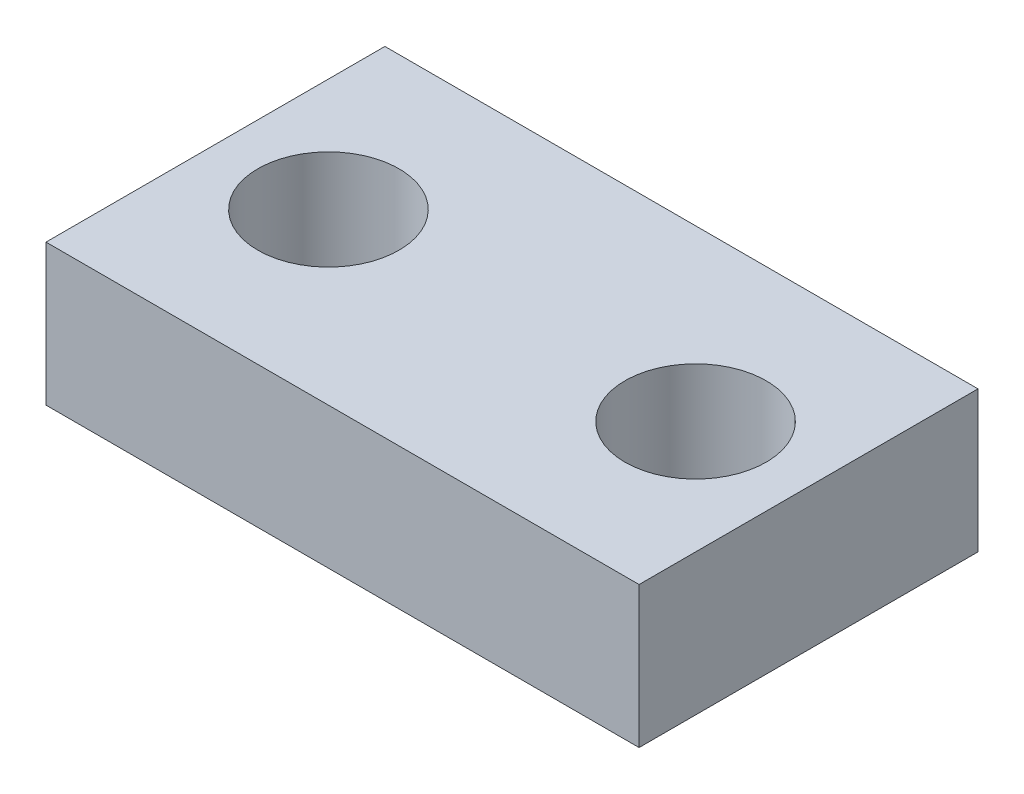
SolidWorks part; units mm, degrees
ref_plane "Front Plane" through (0, 0, 0) normal (0, 0, 1) x (1, 0, 0)
ref_plane "Top Plane" through (0, 0, 0) normal (0, 1, 0) x (1, 0, 0)
ref_plane "Right Plane" through (0, 0, 0) normal (1, 0, 0) x (0, 0, -1)
sketch "Sketch2" plane through (0, 0, 0) normal (0, 1, 0) x (1, 0, 0)
  line L1 (-33.3375, -19.05) -> (33.3375, -19.05)
  line L2 (-33.3375, -19.05) -> (-33.3375, 19.05)
  line L3 (-33.3375, 19.05) -> (33.3375, 19.05)
  line L4 (33.3375, -19.05) -> (33.3375, 19.05)
  line L5 (-33.3375, -19.05) -> (33.3375, 19.05) construction
  line L6 (-33.3375, 19.05) -> (33.3375, -19.05) construction
  point P0 (0, 0)
  dimension "D1" = 66.675
  dimension "D2" = 38.1
extrude "Boss-Extrude1" add sketch "Sketch2" along normal blind 15.875
sketch "Sketch3" plane through (0, 15.875, 0) normal (0, 1, 0) x (1, 0, 0)
  line L0 (-20.6375, 0) -> (20.6375, 0) construction
  line L2 (-33.3375, 19.05) -> (-33.3375, -19.05) construction
  circle A0 centre (-20.6375, 0) radius 7.9375
  circle A1 centre (20.6375, 0) radius 7.9375
  dimension "D1" = 15.875
  dimension "D3" = 12.7
  dimension "D2" = 41.275
extrude "Cut-Extrude1" cut sketch "Sketch3" against normal through all
